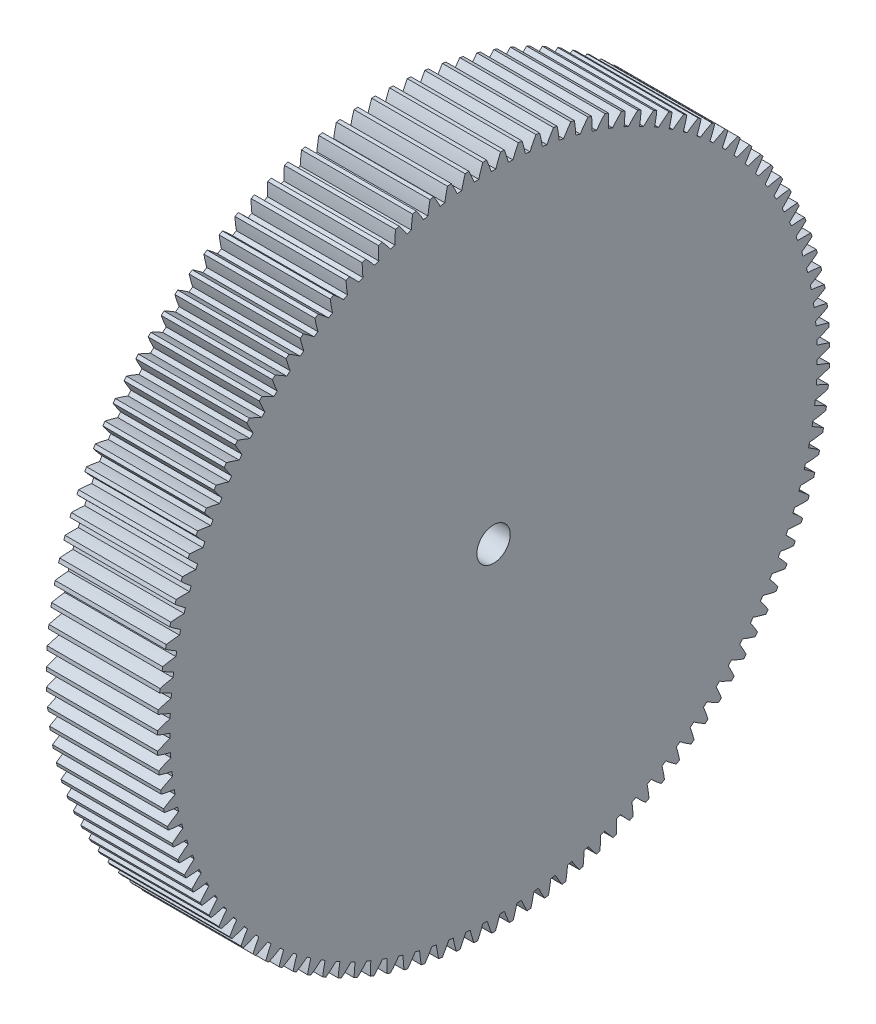
SolidWorks part; units mm, degrees
material "1.0035 (S185)"
ref_plane "Plane1" through (0, 0, 0) normal (0, 0, 1) x (1, 0, 0)
ref_plane "Plane2" through (0, 0, 0) normal (0, 1, 0) x (1, 0, 0)
ref_plane "Plane3" through (0, 0, 0) normal (1, 0, 0) x (0, 0, -1)
sketch "HoldingSke" plane through (0, 0, 0) normal (0, 1, 0) x (1, 0, 0)
  line L0 (0, 0) -> (-0.9696, -1.7492)
  line L1 (-15, 0) -> (100, 0) construction
  line L2 (0, 0) -> (-2.1039, 2.3779)
  line L3 (0, 0) -> (-11.863, 4.5341)
  line L4 (0, 0) -> (-4.1868, 7.5532)
  line L5 (0, 0) -> (-46.8476, -17.4728)
  line L6 (0, 0) -> (-8.2896, -5.593)
  line L7 (-2.1039, 2.3779) -> (8.6586, 51.2059)
  line L8 (-76.2, 54.61) -> (-75.7, 54.61)
  line L9 (-71.009, 38.7566) -> (-53.1078, 45.2721)
  line L10 (-76.2, 71.12) -> (104.1128, 71.12)
  line L11 (0, 0) -> (-10, 0)
  line L12 (-76.2, 101.6) -> (-76.181, 101.6)
  line L13 (24.9733, 27.94) -> (52.9518, 28.4284)
  line L14 (24.9733, 27.94) -> (24.9743, 27.94)
  line L15 (24.9733, 27.94) -> (100.4006, 29.5858)
  line L16 (-63.627, -0.5) -> (-12.827, -0.5)
  circle A0 centre (0, 0) radius 1.5
  circle A1 centre (0, 0) radius 29.124
  circle A2 centre (0, 0) radius 37.5
  circle A3 centre (0, 0) radius 1.5
  dimension "MHD" = 58.248
  dimension "Hub_dia" = 75
  dimension "Bore" = 3
  dimension "MBD" = 3
  dimension "Num_teeth" = 119
  dimension "Pitch_radius" = 180.3128
  dimension "Pitch" = 2
  dimension "Width" = 10
  dimension "Overall_len" = 50
  dimension "Show_teeth" = 119
  dimension "Thickness" = 10
  dimension "OAL" = 50.0001
  dimension "T_dim" = 0.5
  dimension "Ap" = 20
  dimension "H" = 19.05
  dimension "Backlash" = 0.019
  dimension "Addendum_fac" = 1
  dimension "Dedendum_fac" = 1.25
  dimension "Clearance_fac" = 0.25
  dimension "Dedendum_add" = 0.001
  dimension "Module" = 0.5
sketch "BasProSke" plane through (0, 0, 0) normal (0, 1, 0) x (1, 0, 0)
  line L0 (-10, 0) -> (60, 0) construction
  line L1 (0, 0) -> (0, 30.25)
  line L2 (0, 0) -> (10, 0)
  line L3 (10, 0) -> (10, 30.25)
  line L4 (10, 30.25) -> (0, 30.25)
  dimension "Diameter" = 60.5
  dimension "Thickness" = 10
revolve "Base-Revolve" add sketch "BasProSke" angle 360 about L0
sketch "TooCutSke" plane through (0, 0, 0) normal (1, 0, 0) x (0, 0, -1)
  line L1 (0, 0) -> (0, 107) construction
  line L2 (0, 0) -> (-0.4259, 29.747) construction
  line L3 (0, 0) -> (-1.5705, 59.4749) construction
  line L4 (-0.4259, 29.747) -> (-0.7852, 29.7375) construction
  arc A0 (0.2053, 29.1233) -> (-0.2053, 29.1233) centre (0, 0) ccw
  arc A1 (0.6413, 30.2686) -> (-0.6413, 30.2686) centre (0, 0) ccw
  circle A2 centre (0, 0) radius 29.75 construction
  circle A3 centre (0, 0) radius 27.9559 construction
  arc A4 (-0.2053, 29.1233) -> (-0.6413, 30.2686) centre (-11.5298, 25.4675) ccw
  arc A5 (0.6413, 30.2686) -> (0.2053, 29.1233) centre (11.5298, 25.4675) ccw
  dimension "Root_dia" = 58.248
  dimension "Overcut_dia" = 60.5508
  dimension "Pitch_dia" = 59.5
  dimension "Base_dia" = 55.9117
  dimension "Flank_rad" = 11.9
  dimension "Half_ang" = 1.513
  dimension "Half_CT" = 0.3594
extrude "ToothCut" cut sketch "TooCutSke" along normal through all
fillet "Breaks" [suppressed] radius 0.01
fillet "RootFillets" [suppressed] radius 0.126
pattern_circular "TeethCuts" count 119 every 3.025 about axis through (-10, 0, 0) along (1, 0, 0) of "ToothCut", "RootFillets", "Breaks"
sketch "HubNeaOneSke" plane through (0, 0, 0) normal (-1, 0, 0) x (0, 0, 1)
  circle A0 centre (0, 0) radius 29.124
  dimension "Diameter" = 58.248
extrude "HubNearOne" [suppressed] add sketch "HubNeaOneSke" along normal blind 40.0001
sketch "HubNeaBotSke" plane through (0, 0, 0) normal (-1, 0, 0) x (0, 0, 1)
  circle A0 centre (0, 0) radius 29.124
  dimension "Diameter" = 58.248
extrude "HubNearBoth" [suppressed] add sketch "HubNeaBotSke" along normal blind 20
ref_plane "FarPln" through (10, 0, 0) normal (1, 0, 0) x (0, 0, -1)
sketch "HubFarSke" plane through (10, 0, 0) normal (1, 0, 0) x (0, 0, -1)
  circle A0 centre (0, 0) radius 29.124
  dimension "Diameter" = 58.248
extrude "HubFar" [suppressed] add sketch "HubFarSke" along normal blind 20
sketch "BorSke" plane through (0, 0, 0) normal (1, 0, 0) x (0, 0, -1)
  circle A0 centre (0, 0) radius 1.5
  dimension "Diameter" = 3
extrude "Bore" cut sketch "BorSke" along normal mid plane 100.0001
sketch "KeySke" plane through (0, 0, 0) normal (1, 0, 0) x (0, 0, -1)
  line L0 (-0.6, 0) -> (-0.6, 2)
  line L1 (-0.6, 2) -> (0.6, 2)
  line L2 (0.6, 2) -> (0.6, 0)
  line L3 (0, 0) -> (0, 34) construction
  line L4 (-0.6, 0) -> (0.6, 0)
  dimension "Offset" = 2
  dimension "Width" = 1.2
extrude "Keyway" [suppressed] cut sketch "KeySke" along normal mid plane 100.0001
pattern_circular "Keyway2" [suppressed] count 2 every 90 about axis through (-10, 0, 0) along (1, 0, 0)
equation "' \"Module@HoldingSke\" = 6.35"
equation "' \"Num_teeth@HoldingSke\" = 12"
equation "' \"Ap@HoldingSke\" =  20"
equation "' \"Width@HoldingSke\" = 0.5 * 25.4"
equation "' \"Hub_dia@HoldingSke\"= 1 * 25.4"
equation "' \"Overall_len@HoldingSke\" = 1.0 * 25.4"
equation "' \"Bore@HoldingSke\" = 0.75 * 25.4"
equation "' \"T_dim@HoldingSke\" = 0.1 * 25.4"
equation "' \"Width@KeySke\" = 0.25 * 25.4"
equation "' \"Show_teeth@HoldingSke\" = 13"
equation "' \"Backlash@HoldingSke\" = 0.009 * 25.4"
equation "' \"Addendum_fac@HoldingSke\" = 1.0"
equation "' \"Dedendum_fac@HoldingSke\" = 1.25"
equation "' \"Dedendum_add@HoldingSke\" = 0.00005 * 25.4"
equation "' \"Clearance_fac@HoldingSke\" = 0.25"
equation "\"Pitch@HoldingSke\" = 1 / \"Module@HoldingSke\""
equation "\"Overcut_dia@TooCutSke\" = (\"Num_teeth@HoldingSke\" + 2 * \"Addendum_fac@HoldingSke\") / \"Pitch@HoldingSke\" + 0.002 * 25.4"
equation "\"Pitch_dia@TooCutSke\" = \"Num_teeth@HoldingSke\" / \"Pitch@HoldingSke\""
equation "\"Base_dia@TooCutSke\" = \"Num_teeth@HoldingSke\" / \"Pitch@HoldingSke\" * cos((\"Ap@HoldingSke\"  * 3.14159265 / 180))"
equation "\"Root_dia@TooCutSke\" = (\"Num_teeth@HoldingSke\" + 2) / \"Pitch@HoldingSke\" - 2 * (\"Addendum_fac@HoldingSke\" + \"Dedendum_fac@HoldingSke\") / \"Pitch@HoldingSke\" - \"Dedendum_add@HoldingSke\" * 2"
equation "\"Half_ang@TooCutSke\" = 180 / \"Num_teeth@HoldingSke\""
equation "\"Half_CT@TooCutSke\" = \"Num_teeth@HoldingSke\" / \"Pitch@HoldingSke\" * sin((3.14159265 / 2 / \"Num_teeth@HoldingSke\")) / 2 - 7 * \"Backlash@HoldingSke\" / 4"
equation "\"Flank_rad@TooCutSke\" = \"Num_teeth@HoldingSke\" / \"Pitch@HoldingSke\" / 5"
equation "\"Radius@RootFillets\" = \"Clearance_fac@HoldingSke\" / \"Pitch@HoldingSke\" + \"Dedendum_add@HoldingSke\""
equation "\"Break_rad@Breaks\" = 0.02 / \"Pitch@HoldingSke\""
equation "\"Thickness@HoldingSke\" = \"Width@HoldingSke\""
equation "\"OAL@HoldingSke\" = \"Thickness@HoldingSke\""
equation "\"MHD@HoldingSke\" = (\"Num_teeth@HoldingSke\" + 2) / \"Pitch@HoldingSke\" - 2 * (\"Addendum_fac@HoldingSke\" + \"Dedendum_fac@HoldingSke\")  / \"Pitch@HoldingSke\" - \"Dedendum_add@HoldingSke\" * 2"
equation "\"MBD@HoldingSke\" = (\"Num_teeth@HoldingSke\" + 2) / \"Pitch@HoldingSke\" - 2 * (\"Addendum_fac@HoldingSke\" + \"Dedendum_fac@HoldingSke\")  / \"Pitch@HoldingSke\" - \"Dedendum_add@HoldingSke\" * 2 - 0.002 * 25.4"
equation "\"MHD@HoldingSke\" = ((sgn( \"MHD@HoldingSke\" - \"Hub_dia@HoldingSke\" )-1)*( \"MHD@HoldingSke\" - \"Hub_dia@HoldingSke\" ))/-2+ \"Hub_dia@HoldingSke\""
equation "\"MBD@HoldingSke\" = ((sgn( \"MBD@HoldingSke\" - \"Bore@HoldingSke\" )-1)*( \"MBD@HoldingSke\" - \"Bore@HoldingSke\" ))/-2+ \"Bore@HoldingSke\""
equation "\"OAL@HoldingSke\" = ((sgn( \"OAL@HoldingSke\" - \"Overall_len@HoldingSke\" )+1)*( \"OAL@HoldingSke\" - \"Overall_len@HoldingSke\" ))/2 + \"Overall_len@HoldingSke\" + 0.000002 * 25.4"
equation "\"Num_teeth@TeethCuts\" = int( \"Show_teeth@HoldingSke\" ) + 1"
equation "\"Num_teeth@TeethCuts\" = ((sgn( \"Num_teeth@TeethCuts\" - \"Num_teeth@HoldingSke\" )-1)*( \"Num_teeth@TeethCuts\" - \"Num_teeth@HoldingSke\" ))/-2+ \"Num_teeth@HoldingSke\""
equation "\"Num_teeth@TeethCuts\" = ((sgn( \"Num_teeth@TeethCuts\" - 2.0)+1)*( \"Num_teeth@TeethCuts\" - 2.0))/2 +2.0"
equation "\"Angle@TeethCuts\" = 360.0 / \"Num_teeth@HoldingSke\""
equation "\"Diameter@BasProSke\" = (\"Num_teeth@HoldingSke\" + 2 * \"Addendum_fac@HoldingSke\") / \"Pitch@HoldingSke\""
equation "\"Thickness@BasProSke\"  = \"Thickness@HoldingSke\""
equation "' \"Fillet_rad@BasProSke\" =  \"Thickness@HoldingSke\" * 0.05"
equation "\"MHD@HoldingSke\" = ((sgn( \"MHD@HoldingSke\" - \"Root_dia@TooCutSke\" )-1)*( \"MHD@HoldingSke\" - \"Root_dia@TooCutSke\" ))/-2+ \"Root_dia@TooCutSke\""
equation "\"Diameter@HubNeaOneSke\" = \"MHD@HoldingSke\""
equation "\"Length@HubNearOne\" = \"OAL@HoldingSke\" - \"Thickness@BasProSke\""
equation "\"Diameter@HubNeaBotSke\" = \"MHD@HoldingSke\""
equation "\"Length@HubNearBoth\" = ( \"OAL@HoldingSke\" - \"Thickness@BasProSke\" ) / 2.0"
equation "\"Thickness@FarPln\" = \"Thickness@BasProSke\""
equation "\"Diameter@HubFarSke\" = \"MHD@HoldingSke\""
equation "\"Length@HubFar\" = ( \"OAL@HoldingSke\" - \"Thickness@BasProSke\" ) / 2.0"
equation "\"Diameter@BorSke\" = \"MBD@HoldingSke\""
equation "\"D1@Bore\" = \"OAL@HoldingSke\" * 2.0"
equation "\"D1@Keyway\" = \"OAL@HoldingSke\" * 2.0"
equation "\"Offset@KeySke\" = \"T_dim@HoldingSke\" + \"MBD@HoldingSke\" / 2.0"
